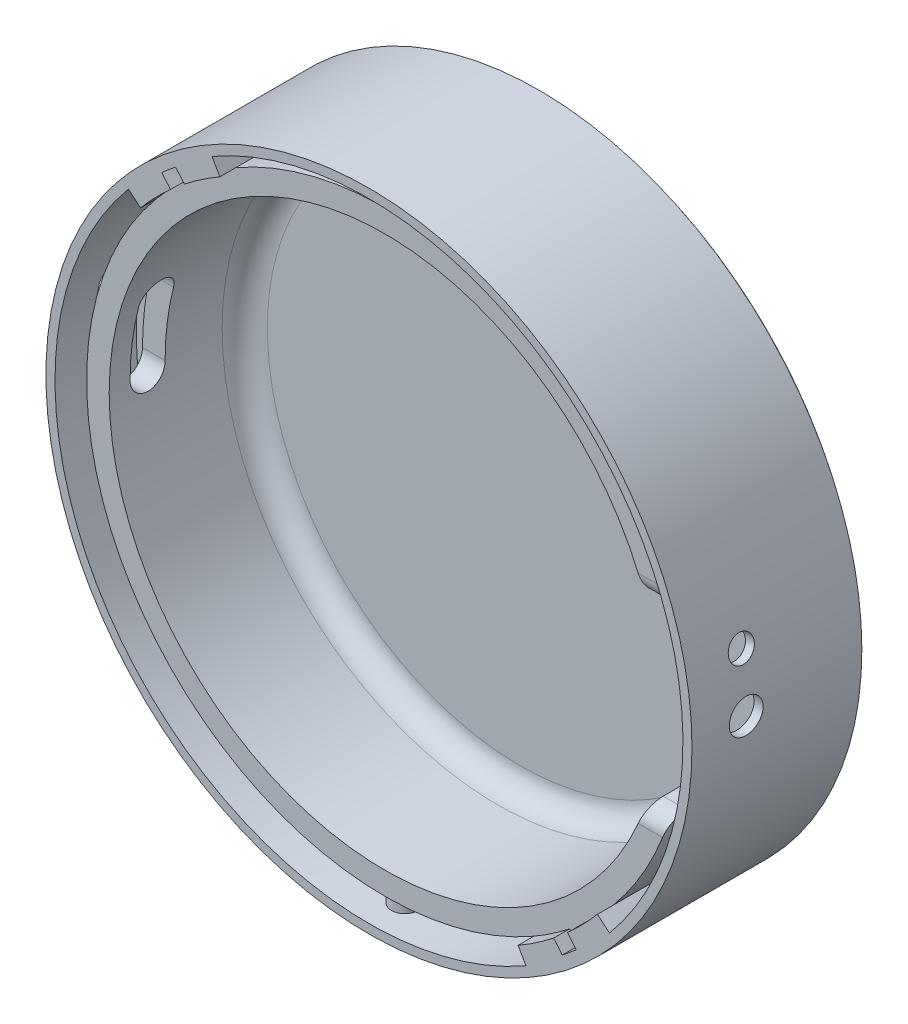
SolidWorks part; units mm, degrees
ref_plane "Alzado" through (0, 0, 0) normal (0, 0, 1) x (1, 0, 0)
ref_plane "Planta" through (0, 0, 0) normal (0, 1, 0) x (1, 0, 0)
ref_plane "Vista lateral" through (0, 0, 0) normal (1, 0, 0) x (0, 0, -1)
sketch "Croquis1" plane through (0, 0, 0) normal (0, 0, 1) x (1, 0, 0)
  circle A0 centre (0, 0) radius 75
  dimension "D1" = 150
extrude "Saliente-Extruir1" add sketch "Croquis1" against normal blind 40
sketch "Croquis2" plane through (0, 0, 0) normal (0, 0, 1) x (1, 0, 0)
  circle A0 centre (0, 0) radius 66
  dimension "D1" = 132
extrude "Cortar-Extruir1" cut sketch "Croquis2" against normal blind 3.5
sketch "Croquis3" plane through (0, 0, -3.5) normal (0, 0, 1) x (1, 0, 0)
  circle A0 centre (0, 0) radius 61
  dimension "D1" = 122
extrude "Cortar-Extruir2" cut sketch "Croquis3" against normal blind 30
sketch "Croquis4" plane through (0, 0, 0) normal (0, 0, 1) x (1, 0, 0)
  circle A0 centre (0, 0) radius 66
  circle A1 centre (0, 0) radius 69.5
  dimension "D1" = 132
  dimension "D2" = 139
extrude "Cortar-Extruir3" cut sketch "Croquis4" against normal blind 18
sketch "Croquis5" plane through (0, 0, 0) normal (0, 1, 0) x (1, 0, 0)
  circle A0 centre (0, 8) radius 3
  dimension "D2" = 6
  dimension "D1" = 8
extrude "Saliente-Extruir2" add sketch "Croquis5" along normal mid plane 140
sketch "Croquis6" plane through (0, 0, -3.5) normal (0, 0, 1) x (1, 0, 0)
  circle A0 centre (0, 0) radius 61
extrude "Cortar-Extruir4" cut sketch "Croquis6" against normal up to surface (30 mm away) up to face at (61, 0, -33.5)
fillet "Redondeo1" radius 10 1 edges at (75, 0, -40)
fillet "Redondeo2" radius 5 1 edges at (61, 0, -33.5)
sketch "Croquis7" plane through (0, 0, 0) normal (0, 0, 1) x (1, 0, 0)
  line L0 (63.6982, 20) -> (30, 20)
  line L1 (30, 20) -> (30, -20)
  line L2 (30, -20) -> (63.6982, -20)
  line L3 (0, -22) -> (0, 22) construction
  line L4 (22, 0) -> (-22, 0) construction
  arc A0 (63.6982, -20) -> (63.6982, 20) centre (0, 0) ccw
  dimension "D1" = 30
  dimension "D2" = 20
  dimension "D3" = 20
extrude "Cortar-Extruir5" cut sketch "Croquis7" against normal blind 18
sketch "Croquis8" plane through (0, 0, 0) normal (1, 0, 0) x (0, 0, -1)
  line L0 (18, 20) -> (18, -20) construction
  circle A0 centre (12, 0) radius 3.75
  dimension "D2" = 7.5
  dimension "D1" = 6
extrude "Cortar-Extruir6" cut sketch "Croquis8" along normal mid plane 192
ref_plane "Plano1" through (73.8606, 13.0236, 0) normal (0.9848, 0.1736, 0) x (0, 0, 1)
sketch "Croquis10" plane through (73.8606, 13.0236, 0) normal (0.9848, 0.1736, 0) x (0, 0, 1)
  circle A0 centre (-12, 0) radius 2.85
  dimension "D2" = 5.7
  dimension "D1" = 6
extrude "Cortar-Extruir7" cut sketch "Croquis10" against normal blind 52
fillet "Redondeo3" radius 4 4 edges at (60.2624, 20, -3.5) (60.2624, 20, -18) (60.2624, -20, -18) (60.2624, -20, -3.5)
sketch "Croquis11" plane through (0, 0, 0) normal (0, 0, 1) x (1, 0, 0)
  line L0 (-35.6312, 61.7151) -> (-33, 57.1577)
  line L1 (-54.5902, 45.8066) -> (-50.5589, 42.424)
  line L2 (57.6281, -20) -> (62.8967, -20) construction
  line L3 (50.5589, -42.424) -> (54.5902, -45.8066)
  line L4 (33, -57.1577) -> (35.6312, -61.7151)
  arc A0 (-35.6312, 61.7151) -> (-54.5902, 45.8066) centre (0, 0) ccw
  arc A1 (-33, 57.1577) -> (-50.5589, 42.424) centre (0, 0) ccw
  arc A2 (35.6312, -61.7151) -> (54.5902, -45.8066) centre (0, 0) ccw
  arc A3 (33, -57.1577) -> (50.5589, -42.424) centre (0, 0) ccw
  dimension "D3" = 66
  dimension "D1" = 20
  dimension "D2" = 40
extrude "Saliente-Extruir3" add sketch "Croquis11" against normal blind 22
sketch "Croquis12" plane through (0, 0, 0) normal (0, 0, 1) x (1, 0, 0)
  line L0 (42.424, -50.5589) -> (-42.424, 50.5589)
  line L1 (45.8658, -51.5493) -> (-42.8016, 54.1204)
  line L2 (42.8016, -54.1204) -> (-45.8658, 51.5493)
  arc A0 (-42.8016, 54.1204) -> (-45.8658, 51.5493) centre (0, 0) ccw
  arc A1 (33, -57.1577) -> (50.5589, -42.424) centre (0, 0) ccw construction
  arc A2 (-33, 57.1577) -> (-50.5589, 42.424) centre (0, 0) ccw construction
  arc A3 (42.8016, -54.1204) -> (45.8658, -51.5493) centre (0, 0) ccw
  arc M5 (-50.5589, 42.424) -> (-33, 57.1577) centre (0, 0) cw
  arc M9 (50.5589, -42.424) -> (33, -57.1577) centre (0, 0) cw
  dimension "D3" = 138
  dimension "D1" = 2
  dimension "D2" = 2
extrude "Cortar-Extruir9" cut sketch "Croquis12" against normal blind 3.5 contours L2 L0 M9 M5
sketch "Croquis13" plane through (0, 0, 0) normal (0, 0, 1) x (1, 0, 0)
  circle A0 centre (0, 0) radius 75
  circle A1 centre (0, 0) radius 71.5
  dimension "D1" = 143
extrude "Cortar-Extruir10" cut sketch "Croquis13" against normal blind 61
scale "Escala1" scale about centroid uniform scaling yes scale factor 0.8
ref_plane "Plano2" through (-57.5, 0, 0) normal (1, 0, 0) x (0, 0, -1)
sketch "Croquis14" plane through (-57.5, 0, 0) normal (1, 0, 0) x (0, 0, -1)
  line L0 (15.1479, 3.0994) -> (15.1479, -0.0006)
  line L2 (12.0479, -0.0006) -> (12.0479, 11.9994)
  line L4 (18.2479, 11.9994) -> (18.2479, -1.2565)
  arc A0 (12.0479, -0.0006) -> (18.2479, -0.0006) centre (15.1479, -0.0006) ccw
  arc A1 (18.2479, 11.9994) -> (12.0479, 11.9994) centre (15.1479, 11.9994) ccw
  dimension "D1" = 6.2
  dimension "D2" = 6.2
  dimension "D3" = 12
extrude "Cortar-Extruir13" cut sketch "Croquis14" along normal blind 16
